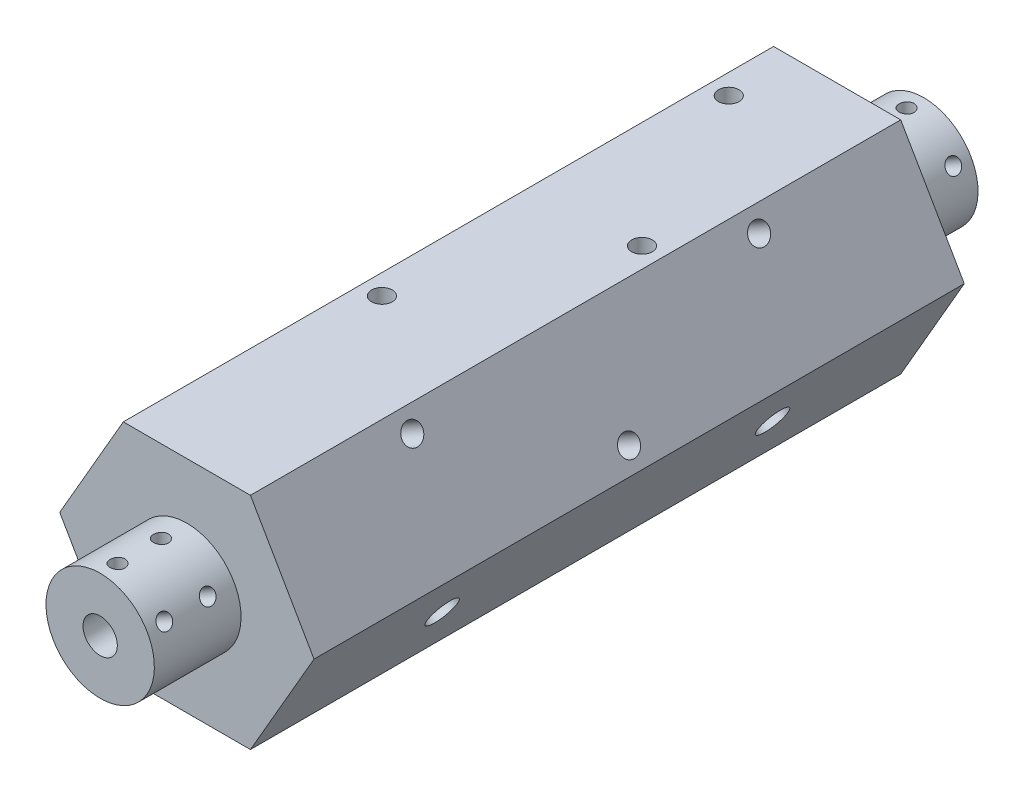
SolidWorks part; units mm, degrees
material "6061-T6 (SS)"
ref_plane "Front Plane" through (0, 0, 0) normal (0, 0, 1) x (1, 0, 0)
ref_plane "Top Plane" through (0, 0, 0) normal (0, 1, 0) x (1, 0, 0)
ref_plane "Right Plane" through (0, 0, 0) normal (1, 0, 0) x (0, 0, -1)
ref_axis "Axis1" through (0, 0, -110) along (0, 0, 1)
sketch "Sketch1" plane through (0, 0, 0) normal (0, 0, 1) x (1, 0, 0)
  line L0 (-14.6647, 25.4) -> (14.6647, 25.4)
  line L1 (-14.6647, 25.4) -> (-29.3294, 0)
  line L2 (-14.6647, -25.4) -> (14.6647, -25.4)
  line L3 (14.6647, 25.4) -> (29.3294, 0)
  line L4 (29.3294, 0) -> (14.6647, -25.4)
  line L5 (-29.3294, 0) -> (-14.6647, -25.4)
  circle A0 centre (0, 0) radius 10 construction
  circle A1 centre (0, 0) radius 25.4 construction
  dimension "D2" = 20
  dimension "D1" = 50.8
  dimension "D3" = 60
extrude "Boss-Extrude1" add sketch "Sketch1" along normal mid plane 190
hole_wizard "N (0.302) Diameter Hole1" positions "Sketch5" profile "Sketch4" hole size "N" standard "Ansi Inch"
sketch "Sketch5" plane through (0, 0, -95) normal (0, 0, -1) x (-1, 0, 0)
  point P0 (0, 0)
sketch "Sketch4" plane through (0, 0, -95) normal (1, 0, 0) x (0, 1, 0)
  line L0 (0, 0) -> (0, 28.8354)
  line L1 (0, 28.8354) -> (3.8354, 25)
  line L2 (3.8354, 25) -> (3.8354, 0)
  line L5 (3.8354, 0) -> (0, 0)
  line L10 (0, 28.8354) -> (-3.8354, 25) construction
  line L11 (0, -6.35) -> (0, 107.95) construction
  dimension "Hole Dia." = 7.6708
  dimension "Hole Depth" = 25
  dimension "Drill Angle" = 90
sketch "Sketch7" plane through (0, 0, 0) normal (1, 0, 0) x (0, 0, -1)
  line L0 (95, 12.5) -> (75, 12.5)
  line L2 (95, 12.5) -> (95, 40)
  line L3 (95, 0) -> (95, 3.9575)
  line L7 (72, 3.9575) -> (95, 3.9575)
  line L8 (72, 3.9575) -> (72, 0)
  line L9 (72, 0) -> (95, 0)
  line L11 (110.1624, 0) -> (105.4354, 0) construction
  line L13 (75, 12.5) -> (75, 40)
  line L14 (75, 40) -> (95, 40)
  dimension "D1" = 7.915
  dimension "D3" = 25
  dimension "D4" = 40
  dimension "D6" = 20
  dimension "D9" = 23
revolve "Cut-Revolve1" cut sketch "Sketch7" angle 360 about L11
hole_wizard "#8-32 Tapped Hole1" positions "3DSketch3" profile "Sketch14" tap size "#8-32" standard "Ansi Inch"
sketch3d "3DSketch3"
  line L0 (0, 0, 0) -> (0, 0, -91) construction
  line L1 (0, 0, -91) -> (0, 12.5, -91) construction
  line L4 (0, 0, -81) -> (0, 12.5, -81) construction
  point P0 (0, 12.5, -91)
  point P2 (0, 12.5, -81)
  dimension "D1" = 4
  dimension "D2" = 10
sketch "Sketch14" plane through (0, 12.5, -91) normal (1, 0, 0) x (0, 0, 1)
  line L0 (0, 0) -> (0, 25)
  line L1 (0, 25) -> (1.7272, 25)
  line L2 (1.7272, 25) -> (1.7272, 0)
  line L5 (1.7272, 0) -> (0, 0)
  line L11 (0, -6.35) -> (0, 107.95) construction
  dimension "Thru Tap Drill Dia." = 3.4544
  dimension "Thru Tap Drill Depth" = 25
cosmetic thread "Hole Thread1" parameters "D2"=4.1656
cosmetic thread "Hole Thread2" parameters "D2"=4.1656
pattern_circular "CirPattern1" count 2 over 60 about axis through (0, 0, -110) along (0, 0, 1) of "#8-32 Tapped Hole1"
mirror "Mirror1" about plane through (0, 0, 0) normal (0, 0, 1) of "#8-32 Tapped Hole1", "N (0.302) Diameter Hole1", "Cut-Revolve1", "CirPattern1"
hole_wizard "3/16 (0.1875) Diameter Hole1" positions "3DSketch2" profile "Sketch11" hole size "3/16" standard "Ansi Inch"
sketch3d "3DSketch2"
  line L0 (-10, 25.4, -60) -> (10, 25.4, -60) construction
  line L4 (0, 25.4, -60) -> (0, 25.4, 20) construction
  line L6 (-10, 25.4, 20) -> (10, 25.4, 20) construction
  line L8 (0, 0, 0) -> (0, 25.4, 0) construction
  line L10 (26.997, 4.0397, 40) -> (16.997, 21.3603, 40) construction
  line L12 (26.997, 4.0397, -40) -> (16.997, 21.3603, -40) construction
  line L14 (21.997, 12.7, 40) -> (21.997, 12.7, -40) construction
  line L16 (0, 0, 0) -> (21.997, 12.7, 0) construction
  line L18 (10, -25.4, -20) -> (-10, -25.4, -20) construction
  line L20 (-10, -25.4, 60) -> (10, -25.4, 60) construction
  line L22 (0, -25.4, -20) -> (0, -25.4, 60) construction
  line L24 (0, 0, 0) -> (0, -25.4, 0) construction
  line L27 (10, 25.4, 20) -> (10, 25.4, -60) construction
  line L29 (26.997, 4.0397, 40) -> (26.997, 4.0397, -40) construction
  line L31 (-10, -25.4, 60) -> (-10, -25.4, -20) construction
  line L32 (21.997, 12.7, -40) -> (21.997, 12.7, -60) construction
  line L33 (21.997, 12.7, -60) -> (10, 25.4, -60) construction
  line L35 (0, -25.4, -20) -> (0, -25.4, -40) construction
  line L36 (0, -25.4, -40) -> (26.997, 4.0397, -40) construction
  line L38 (0, -25.4, 60) -> (0, -25.4, 75) construction
  line L39 (14.6647, -25.4, 75) -> (-14.6647, -25.4, 75) construction
  line L41 (0, 25.4, -60) -> (0, 25.4, -75) construction
  line L42 (14.6647, 25.4, -75) -> (-14.6647, 25.4, -75) construction
  point P0 (-10, 25.4, 20)
  point P2 (-10, 25.4, -60)
  point P4 (10, 25.4, -20)
  point P29 (26.997, 4.0397, 0)
  point P31 (16.997, 21.3603, -40)
  point P48 (16.997, 21.3603, 40)
  point P52 (10, -25.4, -20)
  point P54 (-10, -25.4, 20)
  point P56 (10, -25.4, 60)
  dimension "D1" = 80
  dimension "D2" = 20
  dimension "D3" = 20
sketch "Sketch11" plane through (-10, 25.4, 20) normal (1, 0, 0) x (0, 0, 1)
  line L0 (0, 0) -> (0, 17.3812)
  line L1 (0, 17.3812) -> (2.3812, 15)
  line L2 (2.3812, 15) -> (2.3812, 0)
  line L5 (2.3812, 0) -> (0, 0)
  line L10 (0, 17.3812) -> (-2.3813, 15) construction
  line L11 (0, -6.35) -> (0, 107.95) construction
  dimension "Hole Dia." = 4.7625
  dimension "Hole Depth" = 15
  dimension "Drill Angle" = 90
hole_wizard "1/8 (0.125) Diameter Hole1" positions "Sketch17" profile "Sketch16" hole size "1/8" standard "Ansi Inch"
sketch "Sketch17" plane through (0, 0, -75) normal (0, 0, -1) x (-1, 0, 0)
  line L0 (0, 0) -> (0, 20)
  line L1 (0, 20) -> (10, 20)
  point P0 (10, 20)
  dimension "D1" = 20
  dimension "D2" = 10
sketch "Sketch16" plane through (-10, 20, -75) normal (1, 0, 0) x (0, 1, 0)
  line L0 (0, 0) -> (0, 5.5875)
  line L1 (0, 5.5875) -> (1.5875, 4)
  line L2 (1.5875, 4) -> (1.5875, 0)
  line L5 (1.5875, 0) -> (0, 0)
  line L10 (0, 5.5875) -> (-1.5875, 4) construction
  line L11 (0, -6.35) -> (0, 107.95) construction
  dimension "Hole Dia." = 3.175
  dimension "Hole Depth" = 4
  dimension "Drill Angle" = 90
hole_wizard "1/4 Clearance Hole1" positions "Sketch19" profile "Sketch18" hole size "1/4" standard "Ansi Inch" end condition through all
sketch "Sketch19" plane through (-21.997, 12.7, 0) normal (-0.866, 0.5, 0) x (0, 0, 1)
  line L0 (-38.1, 0) -> (38.1, 0)
  point P0 (38.1, 0)
  point P3 (-38.1, 0)
  dimension "D1" = 76.2
sketch "Sketch18" plane through (-21.997, 12.7, 38.1) normal (0, 0, 1) x (-0.5, -0.866, 0)
  line L0 (0, 0) -> (0, 63.5)
  line L1 (0, 63.5) -> (3.5712, 63.5)
  line L2 (3.5712, 63.5) -> (3.5712, 0)
  line L5 (3.5712, 0) -> (0, 0)
  line L11 (0, -6.35) -> (0, 107.95) construction
  dimension "Thru Hole Dia." = 7.1425
  dimension "Thru Hole Depth" = 63.5
